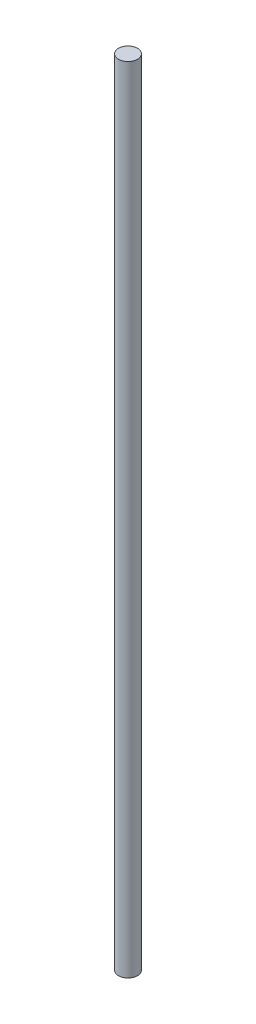
SolidWorks part; units mm, degrees
ref_plane "Front Plane" through (0, 0, 0) normal (0, 0, 1) x (1, 0, 0)
ref_plane "Top Plane" through (0, 0, 0) normal (0, 1, 0) x (1, 0, 0)
ref_plane "Right Plane" through (0, 0, 0) normal (1, 0, 0) x (0, 0, -1)
sketch "Sketch1" plane through (0, 0, 0) normal (0, 1, 0) x (1, 0, 0)
  circle A0 centre (0, 0) radius 6
  dimension "D1" = 12
extrude "Boss-Extrude1" add sketch "Sketch1" along normal blind 500
